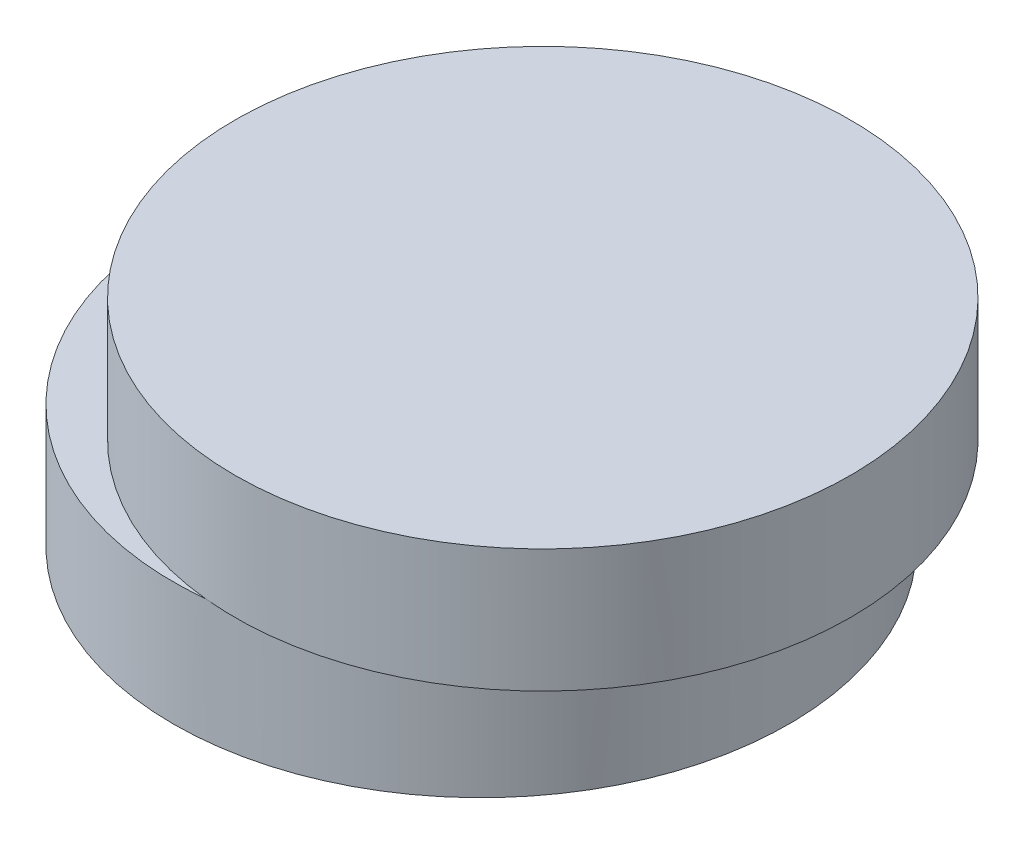
SolidWorks part; units mm, degrees
ref_plane "Front Plane" through (0, 0, 0) normal (0, 0, 1) x (1, 0, 0)
ref_plane "Top Plane" through (0, 0, 0) normal (0, 1, 0) x (1, 0, 0)
ref_plane "Right Plane" through (0, 0, 0) normal (1, 0, 0) x (0, 0, -1)
sketch "Sketch1" plane through (0, 0, 0) normal (0, 1, 0) x (1, 0, 0)
  circle A0 centre (0, 0) radius 5
  dimension "D1" = 10
extrude "Boss-Extrude1" add sketch "Sketch1" along normal blind 2
sketch "Sketch2" plane through (0, 2, 0) normal (0, 1, 0) x (1, 0, 0)
  circle A0 centre (1, 0) radius 5
  circle A1 centre (0, 0) radius 5 construction
  point P5 (0, 0)
  dimension "D1" = 10
  dimension "D2" = 1
extrude "Boss-Extrude2" add sketch "Sketch2" along normal blind 2
